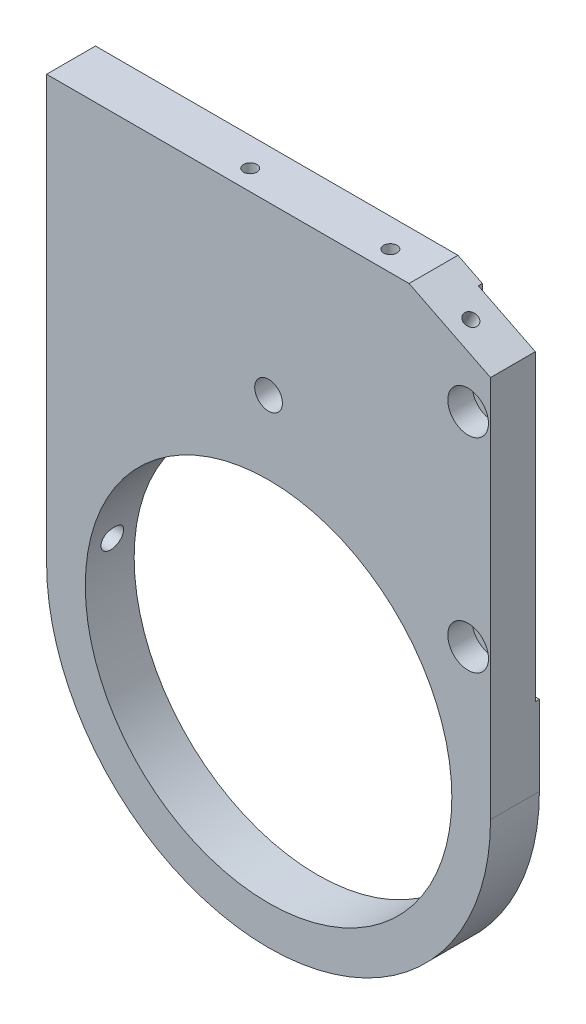
SolidWorks part; units mm, degrees
ref_plane "Alzado" through (0, 0, 0) normal (0, 0, 1) x (1, 0, 0)
ref_plane "Planta" through (0, 0, 0) normal (0, 1, 0) x (1, 0, 0)
ref_plane "Vista lateral" through (0, 0, 0) normal (1, 0, 0) x (0, 0, -1)
sketch "Croquis1" plane through (0, 0, 0) normal (0, 0, 1) x (1, 0, 0)
  line L0 (-54.5, 0) -> (-54.5, 104)
  line L1 (-54.5, 104) -> (34.5, 104)
  line L2 (54.5, 94) -> (54.5, 0)
  line L3 (0, 104.4797) -> (0, 0) construction
  line L4 (34.5, 104) -> (54.5, 94)
  arc A0 (-54.5, 0) -> (54.5, 0) centre (0, 0) ccw
  circle A1 centre (0, 0) radius 45
  dimension "D1" = 54.5
  dimension "D6" = 90
  dimension "D2" = 104
  dimension "D3" = 20
  dimension "D4" = 10
  dimension "D5" = 54.5
extrude "Saliente-Extruir1" add sketch "Croquis1" along normal mid plane 12
hole_wizard "Taladro roscado M41" positions "Croquis3" profile "Croquis2" tap size "M4" standard "DIN"
sketch "Croquis3" plane through (48.5, 97, 0) normal (0.4472, 0.8944, 0) x (-0.8944, 0.4472, 0)
  line L0 (-6.7082, -6) -> (15.6525, -6) construction
  line L1 (-6.7082, 6) -> (-6.7082, -6) construction
  point P0 (4.2918, -1)
  dimension "D1" = 5
  dimension "D2" = 11
sketch "Croquis2" plane through (44.6613, 98.9193, -1) normal (0, 0, 1) x (-0.8944, 0.4472, 0)
  line L0 (0, 0) -> (0, 20.9914)
  line L1 (0, 20.9914) -> (1.65, 20)
  line L2 (1.65, 20) -> (1.65, 0)
  line L5 (1.65, 0) -> (0, 0)
  line L10 (0, 20.9914) -> (-1.65, 20) construction
  line L11 (0, -6.35) -> (0, 107.95) construction
  dimension "Diámetro de perforador para roscar" = 3.3
  dimension "Profundidad de perforador para roscar" = 20
  dimension "Ángulo de perforador" = 118
cosmetic thread "Rosca de taladro1" parameters "D1"=8, "D2"=4
hole_wizard "Taladro roscado M42" positions "Croquis5" profile "Croquis4" tap size "M4" standard "DIN"
sketch "Croquis5" plane through (0, 104, 0) normal (0, 1, 0) x (-1, 0, 0)
  line L0 (-34.5, -6) -> (54.5, -6) construction
  line L1 (54.5, 6) -> (54.5, -6) construction
  point P0 (9.5, -1)
  point P1 (-24.9, -1)
  dimension "D1" = 5
  dimension "D2" = 5
  dimension "D3" = 45
  dimension "D4" = 34.4
sketch "Croquis4" plane through (-9.5, 104, -1) normal (1, 0, 0) x (0, 0, 1)
  line L0 (0, 0) -> (0, 20.9914)
  line L1 (0, 20.9914) -> (1.65, 20)
  line L2 (1.65, 20) -> (1.65, 0)
  line L5 (1.65, 0) -> (0, 0)
  line L10 (0, 20.9914) -> (-1.65, 20) construction
  line L11 (0, -6.35) -> (0, 107.95) construction
  dimension "Diámetro de perforador para roscar" = 3.3
  dimension "Profundidad de perforador para roscar" = 20
  dimension "Ángulo de perforador" = 118
cosmetic thread "Rosca de taladro2" parameters "D1"=8, "D2"=4
cosmetic thread "Rosca de taladro3" parameters "D1"=8, "D2"=4
sketch "Croquis6" plane through (0, 0, 6) normal (0, 0, 1) x (1, 0, 0)
  line L0 (54.5, 0) -> (54.5, 94) construction
  line L1 (40.5, 104) -> (65.6594, 104)
  line L2 (40.5, 104) -> (40.5, 24.6)
  line L3 (45.5, 19.6) -> (65.6594, 19.6)
  line L4 (65.6594, 104) -> (65.6594, 19.6)
  line L5 (34.5, 104) -> (-54.5, 104) construction
  arc A0 (40.5, 24.6) -> (45.5, 19.6) centre (45.5, 24.6) ccw
  dimension "D3" = 5
  dimension "D1" = 14
  dimension "D2" = 84.4
extrude "Cortar-Extruir1" cut sketch "Croquis6" against normal blind 1
sketch "Croquis7" plane through (0, 0, 5) normal (0, 0, 1) x (1, 0, 0)
  line L0 (54.5, 19.6) -> (54.5, 94) construction
  line L1 (34.5, 104) -> (-54.5, 104) construction
  circle A0 centre (49, 84) radius 3.25
  circle A1 centre (49, 34) radius 3.25
  dimension "D4" = 6.5
  dimension "D1" = 5.5
  dimension "D2" = 20
  dimension "D3" = 50
extrude "Cortar-Extruir2" cut sketch "Croquis7" against normal blind 37.7
sketch "Croquis8" plane through (0, 0, -6) normal (0, 0, -1) x (-1, 0, 0)
  circle A0 centre (-49, 84) radius 5
  circle A1 centre (-49, 34) radius 5
  dimension "D1" = 10
extrude "Cortar-Extruir3" cut sketch "Croquis8" against normal blind 6
hole_wizard "Taladro roscado M6x0.51" positions "Croquis11" profile "Croquis10" tap size "M6x0.5" standard "DIN"
sketch "Croquis11" plane through (-54.5, 0, 0) normal (-1, 0, 0) x (0, 0, 1)
  line L0 (6, 104) -> (-6, 104) construction
  point P0 (0, 96.5)
  point P1 (0, 51.7)
  dimension "D1" = 7.5
  dimension "D2" = 44.8
sketch "Croquis10" plane through (-54.5, 96.5, 0) normal (0, 1, 0) x (0, 0, 1)
  line L0 (0, 0) -> (0, 24.1524)
  line L1 (0, 24.1524) -> (2.75, 22.5)
  line L2 (2.75, 22.5) -> (2.75, 0)
  line L5 (2.75, 0) -> (0, 0)
  line L10 (0, 24.1524) -> (-2.75, 22.5) construction
  line L11 (0, -6.35) -> (0, 107.95) construction
  dimension "Diámetro de perforador para roscar" = 5.5
  dimension "Profundidad de perforador para roscar" = 22.5
  dimension "Ángulo de perforador" = 118
cosmetic thread "Rosca de taladro4" parameters "D1"=12, "D2"=6
cosmetic thread "Rosca de taladro5" parameters "D1"=12, "D2"=6
hole_wizard "Taladro roscado M6x0.52" positions "Croquis13" profile "Croquis12" tap size "M6x0.5" standard "DIN"
sketch "Croquis13" plane through (-54.5, 0, 0) normal (-1, 0, 0) x (0, 0, 1)
  point P0 (0, 7.5)
  dimension "D1" = 44.2
sketch "Croquis12" plane through (-54.5, 7.5, 0) normal (0, 1, 0) x (0, 0, 1)
  line L0 (0, 0) -> (0, 12.1524)
  line L1 (0, 12.1524) -> (2.75, 10.5)
  line L2 (2.75, 10.5) -> (2.75, 0)
  line L5 (2.75, 0) -> (0, 0)
  line L10 (0, 12.1524) -> (-2.75, 10.5) construction
  line L11 (0, -6.35) -> (0, 107.95) construction
  dimension "Diámetro de perforador para roscar" = 5.5
  dimension "Profundidad de perforador para roscar" = 10.5
  dimension "Ángulo de perforador" = 118
cosmetic thread "Rosca de taladro6" parameters "D1"=10.5, "D2"=6
hole_wizard "Taladro roscado M81" positions "Croquis16" profile "Croquis15" tap size "M8" standard "DIN" end condition through all
sketch "Croquis16" plane through (0, 0, 6) normal (0, 0, 1) x (1, 0, 0)
  line L0 (-54.5, 104) -> (-54.5, 0) construction
  line L1 (34.5, 104) -> (-54.5, 104) construction
  point P0 (0, 63)
  dimension "D1" = 54.5
  dimension "D2" = 41
sketch "Croquis15" plane through (0, 63, 6) normal (1, 0, 0) x (0, -1, 0)
  line L0 (0, 0) -> (0, 12)
  line L1 (0, 12) -> (3.4, 12)
  line L2 (3.4, 12) -> (3.4, 0)
  line L5 (3.4, 0) -> (0, 0)
  line L11 (0, -6.35) -> (0, 107.95) construction
  dimension "Diámetro de perforador para roscar hasta el siguiente" = 6.8
  dimension "Profundidad de perforador para roscar hasta el siguiente" = 12
cosmetic thread "Rosca de taladro7" parameters "D2"=8
mirror "Simetría1" about plane through (0, 0, -6) normal (0, 0, 1) of bodies 109
delete or keep bodies "Sólido-Eliminar1" type delete bodies bodies 109
